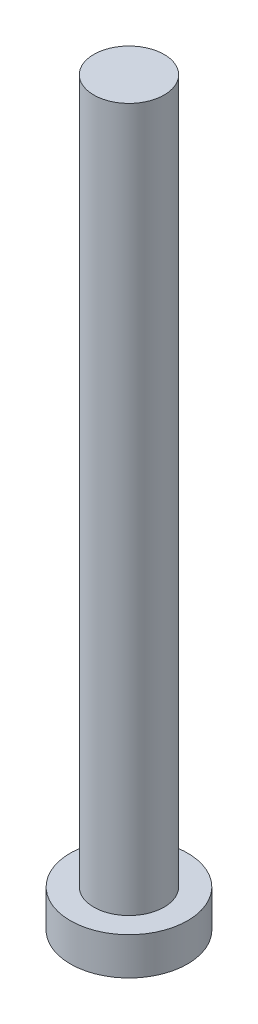
SolidWorks part; units mm, degrees
ref_plane "前视基准面" through (0, 0, 0) normal (0, 0, 1) x (1, 0, 0)
ref_plane "上视基准面" through (0, 0, 0) normal (0, 1, 0) x (1, 0, 0)
ref_plane "右视基准面" through (0, 0, 0) normal (1, 0, 0) x (0, 0, -1)
sketch "草图1" plane through (0, 0, 0) normal (0, 1, 0) x (1, 0, 0)
  circle A0 centre (0, 0) radius 2.5
extrude "凸台-拉伸1" add sketch "草图1" along normal blind 1.6
sketch "草图2" plane through (0, 1.6, 0) normal (0, 1, 0) x (1, 0, 0)
  circle A0 centre (0, 0) radius 1.5
extrude "凸台-拉伸2" add sketch "草图2" along normal blind 30
sketch "草图3" plane through (0, 0, 0) normal (0, -1, 0) x (1, 0, 0)
  line L0 (-0.5, 1) -> (-0.5, 1.75)
  line L1 (-1.75, -0.5) -> (-1, -0.5)
  line L2 (-1.75, -0.5) -> (-1.75, 0.5)
  line L3 (-1.75, 0.5) -> (-1, 0.5)
  line L4 (1.75, -0.5) -> (1.75, 0.5)
  line L5 (-1.75, -0.5) -> (1.75, 0.5) construction
  line L6 (-1.75, 0.5) -> (1.75, -0.5) construction
  line L7 (-0.5, -1.75) -> (0.5, -1.75)
  line L8 (-0.5, -1.75) -> (-0.5, -1)
  line L9 (-0.5, 1.75) -> (0.5, 1.75)
  line L10 (0.5, -1.75) -> (0.5, -1)
  line L11 (-0.5, -1.75) -> (0.5, 1.75) construction
  line L12 (-0.5, 1.75) -> (0.5, -1.75) construction
  line L13 (1, -0.5) -> (1.75, -0.5)
  line L14 (0.5, 1) -> (0.5, 1.75)
  line L15 (1, 0.5) -> (1.75, 0.5)
  arc A0 (1, -0.5) -> (0.5, -1) centre (1, -1) ccw
  arc A1 (-0.5, -1) -> (-1, -0.5) centre (-1, -1) ccw
  arc A2 (0.5, 1) -> (1, 0.5) centre (1, 1) ccw
  arc A3 (-0.5, 1) -> (-1, 0.5) centre (-1, 1) cw
  point P0 (0, 0)
  point P6 (0, 0)
  point P21 (0.5, 0.5)
  dimension "D1" = 0.5
extrude "切除-拉伸1" cut sketch "草图3" against normal blind 1
